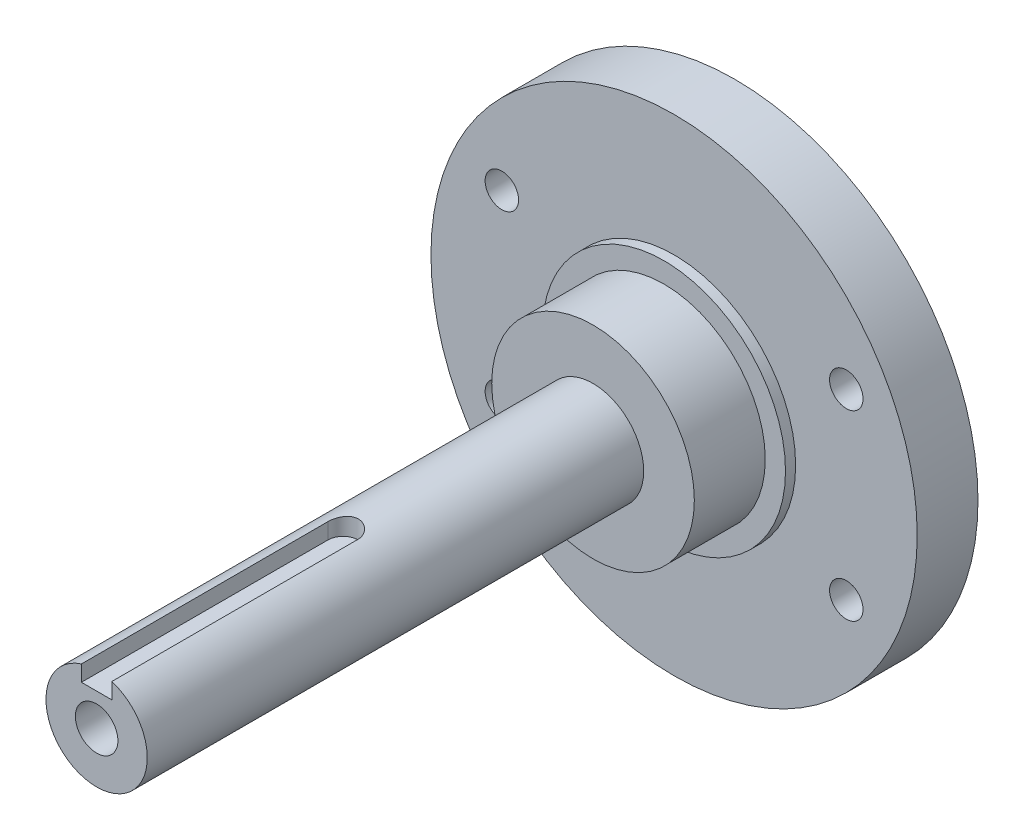
SolidWorks part; units mm, degrees
material "Alumine"
ref_plane "Plan de face" through (0, 0, 0) normal (0, 0, 1) x (1, 0, 0)
ref_plane "Plan de dessus" through (0, 0, 0) normal (0, 1, 0) x (1, 0, 0)
ref_plane "Plan de droite" through (0, 0, 0) normal (1, 0, 0) x (0, 0, -1)
sketch "Esquisse1" plane through (0, 0, 0) normal (0, 0, 1) x (1, 0, 0)
  circle A0 centre (0, 0) radius 12
  dimension "D1" = 24
extrude "Boss.-Extru.1" add sketch "Esquisse1" along normal blind 1
sketch "Esquisse2" plane through (0, 0, 0) normal (0, 0, -1) x (-1, 0, 0)
  circle A0 centre (0, 0) radius 24
  dimension "D1" = 48
extrude "Boss.-Extru.2" add sketch "Esquisse2" along normal blind 6
hole_wizard "Trou pour taraudage pour trou taraudé M42" positions "Esquisse5" profile "Esquisse6" hole size "M4" standard "ISO"
sketch "Esquisse5" plane through (0, 0, -6) normal (0, 0, -1) x (-1, 0, 0)
  line L6 (17, -9) -> (-17, -9) construction
  line L7 (17, -9) -> (17, 9) construction
  line L8 (17, 9) -> (-17, 9) construction
  line L9 (-17, -9) -> (-17, 9) construction
  line L10 (17, -9) -> (-17, 9) construction
  line L11 (17, 9) -> (-17, -9) construction
  point P50 (-17, 9)
  point P107 (17, -9)
  point P108 (17, 9)
  point P109 (-17, -9)
  dimension "D1" = 34
  dimension "D2" = 18
sketch "Esquisse6" plane through (17, 9, -6) normal (1, 0, 0) x (0, 1, 0)
  line L0 (0, 0) -> (0, 6.9914)
  line L1 (0, 6.9914) -> (1.65, 6)
  line L2 (1.65, 6) -> (1.65, 0)
  line L5 (1.65, 0) -> (0, 0)
  line L10 (0, 6.9914) -> (-1.65, 6) construction
  line L11 (0, -6.35) -> (0, 107.95) construction
  dimension "Diamètre du perçage" = 3.3
  dimension "Profondeur du perçage" = 6
  dimension "Angle de pointe" = 118
sketch "Esquisse12" plane through (0, 0, 1) normal (0, 0, 1) x (1, 0, 0)
  circle A0 centre (0, 0) radius 5
  dimension "D1" = 10
extrude "Boss.-Extru.3" add sketch "Esquisse12" along normal blind 56
hole_wizard "Trou pour taraudage pour trou taraudé M51" positions "Esquisse14" profile "Esquisse15" hole size "M5" standard "ISO"
sketch "Esquisse14" plane through (0, 0, 57) normal (0, 0, 1) x (1, 0, 0)
  point P0 (0, 0)
sketch "Esquisse15" plane through (0, 0, 57) normal (1, 0, 0) x (0, -1, 0)
  line L0 (0, 0) -> (0, 21.2618)
  line L1 (0, 21.2618) -> (2.1, 20)
  line L2 (2.1, 20) -> (2.1, 0)
  line L5 (2.1, 0) -> (0, 0)
  line L10 (0, 21.2618) -> (-2.1, 20) construction
  line L11 (0, -6.35) -> (0, 107.95) construction
  dimension "Diamètre du perçage" = 4.2
  dimension "Profondeur du perçage" = 20
  dimension "Angle de pointe" = 118
sketch "Esquisse16" plane through (0, 0, 0) normal (0, 1, 0) x (1, 0, 0)
  line L0 (0, -57) -> (0, -32.67) construction
  line L1 (-5, -57) -> (5, -57) construction
  line L2 (-1.5, -57) -> (-1.5, -32.67)
  line L3 (1.5, -57) -> (1.5, -32.67)
  arc A0 (-1.5, -57) -> (1.5, -57) centre (0, -57) ccw
  arc A1 (1.5, -32.67) -> (-1.5, -32.67) centre (0, -32.67) ccw
  point P5 (0, -44.835)
  dimension "D1" = 1.5
extrude "Enlèv. mat.-Extru.3" cut sketch "Esquisse16" along normal through all from offset 3.2
sketch "Esquisse19" plane through (0, 0, 1) normal (0, 0, 1) x (1, 0, 0)
  circle A0 centre (0, 0) radius 10
  dimension "D1" = 20
extrude "Boss.-Extru.4" add sketch "Esquisse19" along normal blind 7
